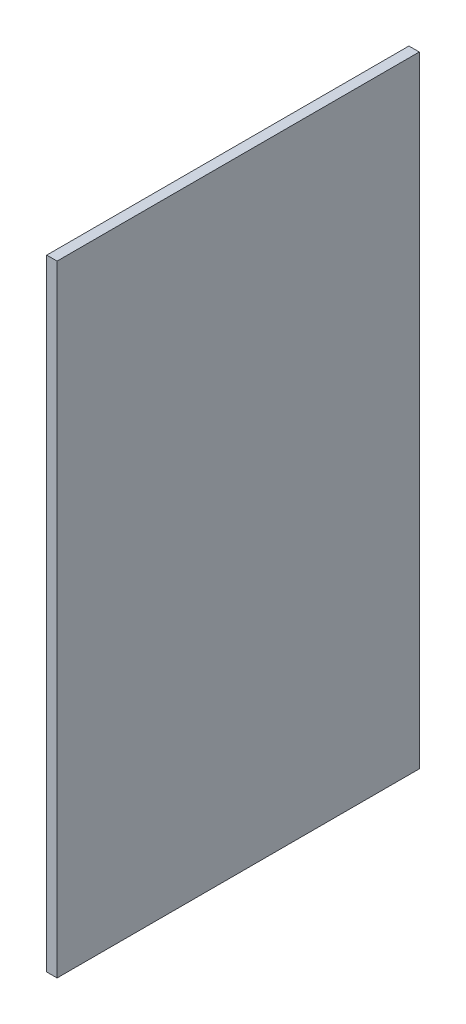
SolidWorks part; units mm, degrees
ref_plane "Front Plane" through (0, 0, 0) normal (0, 0, 1) x (1, 0, 0)
ref_plane "Top Plane" through (0, 0, 0) normal (0, 1, 0) x (1, 0, 0)
ref_plane "Right Plane" through (0, 0, 0) normal (1, 0, 0) x (0, 0, -1)
sketch "Sketch1" plane through (0, 0, 0) normal (0, 1, 0) x (1, 0, 0)
  line L1 (-1, -35) -> (1, -35)
  line L2 (-1, -35) -> (-1, 35)
  line L3 (-1, 35) -> (1, 35)
  line L4 (1, -35) -> (1, 35)
  line L5 (-1, -35) -> (1, 35) construction
  line L6 (-1, 35) -> (1, -35) construction
  point P0 (0, 0)
  dimension "D1" = 70
  dimension "D2" = 2
extrude "Boss-Extrude1" add sketch "Sketch1" along normal blind 120 contours L2 L3 L4 L1
